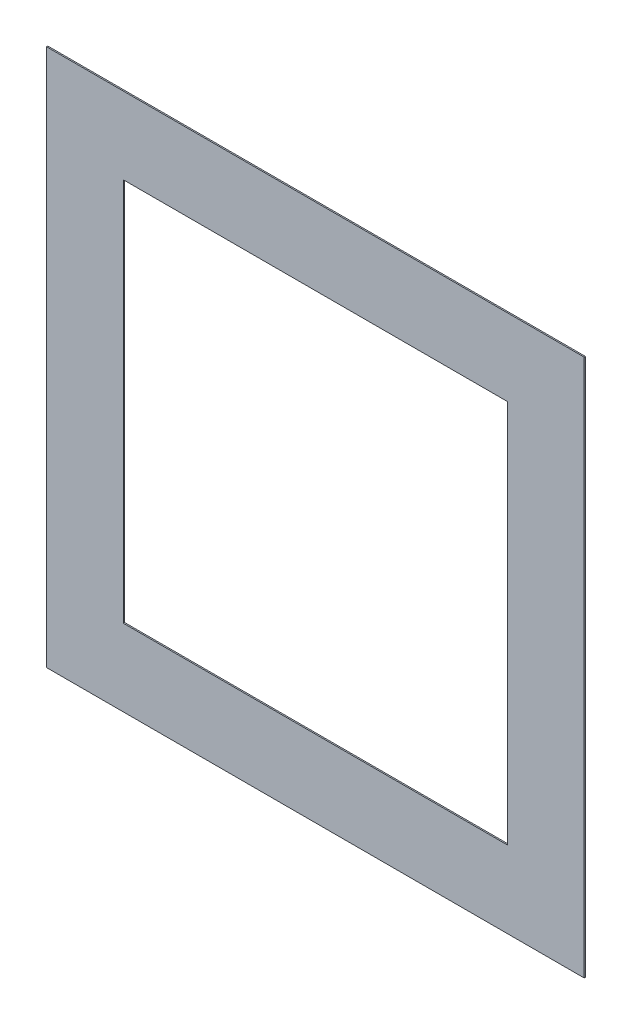
SolidWorks part; units mm, degrees
ref_plane "Front Plane" through (0, 0, 0) normal (0, 0, 1) x (1, 0, 0)
ref_plane "Top Plane" through (0, 0, 0) normal (0, 1, 0) x (1, 0, 0)
ref_plane "Right Plane" through (0, 0, 0) normal (1, 0, 0) x (0, 0, -1)
sketch "Sketch1" plane through (0, 0, 0) normal (0, 0, 1) x (1, 0, 0)
  line L1 (-994.5205, 571.2329) -> (1105.4795, 571.2329)
  line L2 (-994.5205, 571.2329) -> (-994.5205, -1528.7671)
  line L3 (-994.5205, -1528.7671) -> (1105.4795, -1528.7671)
  line L4 (1105.4795, 571.2329) -> (1105.4795, -1528.7671)
  dimension "D1" = 2100
  dimension "D2" = 2100
extrude "Boss-Extrude1" add sketch "Sketch1" along normal blind 5
sketch "Sketch2" plane through (0, 0, 5) normal (0, 0, 1) x (1, 0, 0)
  line L0 (1105.4795, 571.2329) -> (-994.5205, 571.2329) construction
  line L1 (-694.5205, 271.2329) -> (805.4795, 271.2329)
  line L2 (-694.5205, 271.2329) -> (-694.5205, -1228.7671)
  line L3 (-694.5205, -1228.7671) -> (805.4795, -1228.7671)
  line L4 (805.4795, 271.2329) -> (805.4795, -1228.7671)
  line L6 (1105.4795, -1528.7671) -> (1105.4795, 571.2329) construction
  dimension "D1" = 1500
  dimension "D2" = 1500
  dimension "D3" = 300
  dimension "D4" = 300
extrude "Cut-Extrude1" cut sketch "Sketch2" against normal through all contours L2 L1 L4 L3
sketch "Sketch3" plane through (0, 0, 5) normal (0, 0, 1) x (1, 0, 0)
  line L0 (-994.5205, 571.2329) -> (-994.5205, -1528.7671) construction
  line L1 (-994.5205, 571.2329) -> (1105.4795, 571.2329)
  line L2 (-994.5205, 571.2329) -> (-994.5205, -1528.7671)
  line L3 (-994.5205, -1528.7671) -> (1105.4795, -1528.7671)
  line L4 (1105.4795, 571.2329) -> (1105.4795, -1528.7671)
  line L5 (-811.1429, -989.3866) -> (-92.4762, -989.3866) construction
  dimension "D1" = 0
  dimension "D2" = 0
  dimension "D3" = 2100
  dimension "D4" = 2100
